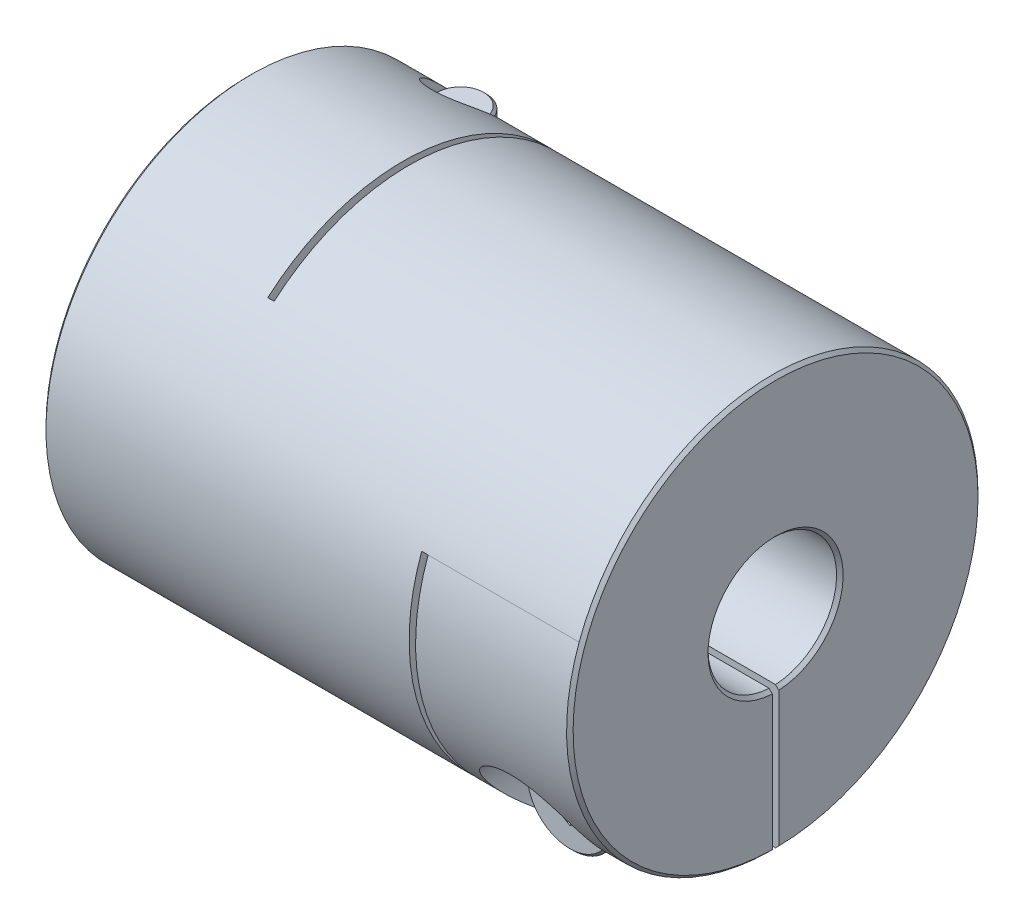
SolidWorks part; units mm, degrees
ref_plane "Front Plane" through (0, 0, 0) normal (0, 0, 1) x (1, 0, 0)
ref_plane "Top Plane" through (0, 0, 0) normal (0, 1, 0) x (1, 0, 0)
ref_plane "Right Plane" through (0, 0, 0) normal (1, 0, 0) x (0, 0, -1)
sketch "Sketch1" plane through (0, 0, 0) normal (1, 0, 0) x (0, 0, -1)
  circle A0 centre (0, 0) radius 16
  dimension "dim D" = 32
extrude "Boss-Extrude1" add sketch "Sketch1" along normal mid plane 41
sketch "Sketch2" plane through (20.5, 0, 0) normal (1, 0, 0) x (0, 0, -1)
  circle A0 centre (0, 0) radius 5
  dimension "dim D1" = 10
extrude "Cut-Extrude1" cut sketch "Sketch2" against normal through all
chamfer "Chamfer1" distance 0.254 angle 45 4 edges at (-20.5, 0, -5) (-20.5, 0, -16) (20.5, 0, -16) (20.5, 0, -5)
ref_plane "Plane2" through (0, -16, 0) normal (0, -1, 0) x (1, 0, 0)
ref_plane "L1" through (-14.5, 0, 0) normal (-1, 0, 0) x (0, 0, 1)
sketch "Sketch4" plane through (0, -16, 0) normal (0, -1, 0) x (1, 0, 0)
  line L0 (-20.246, -16) -> (20.246, -16) construction
  line L1 (-8.5, -16) -> (-8, -16)
  line L2 (-8.5, -16) -> (-8.5, 10.5)
  line L3 (-8.5, 10.5) -> (-8, 10.5)
  line L4 (-8, -16) -> (-8, 10.5)
  line L5 (-8.5, 5) -> (-8.5, 16) construction
  line L6 (20.246, 5) -> (-20.246, 5) construction
  line L7 (20.246, 16) -> (-20.246, 16) construction
  line L10 (-8.5, 10.5) -> (-20.5, 10.5) construction
  line L11 (-20.5, 15.746) -> (-20.5, -15.746) construction
  line L12 (-14.5, 10.2256) -> (-14.5, -10.2256) construction
  point P16 (-14.5, 10.5)
  dimension "D1" = 0.5
extrude "Cut-Extrude2" cut sketch "Sketch4" against normal through all
ref_plane "Plane4" through (0, 0, -16) normal (0, 0, -1) x (-1, 0, 0)
sketch "Sketch7" plane through (0, 0, -16) normal (0, 0, -1) x (-1, 0, 0)
  line L1 (-8, -16) -> (-8.5, -16)
  line L2 (-8.5, -16) -> (-8.5, 5.5)
  line L3 (-8.5, 5.5) -> (-8, 5.5)
  line L4 (-8, -16) -> (-8, 5.5)
  line L5 (20.5, 8.6487) -> (14.5, 8.6487) construction
  line L7 (-10.505, -16) -> (10.505, -16) construction
  line L8 (-20.246, -5) -> (8, -5) construction
  line L9 (20.5, -15.746) -> (20.5, 15.746) construction
  line L10 (-20.246, -5) -> (8, -5) construction
  line L11 (8, 12.0727) -> (8.5, 12.0727) construction
  line L12 (-8.5, 5.5) -> (-8.5, -16) construction
  line L14 (-20.246, -5) -> (8, -5) construction
  line L16 (-20.246, -5) -> (8, -5) construction
  line L17 (8.5, -16) -> (20.246, -16) construction
  line L18 (14.5, -10.2256) -> (14.5, 10.2256) construction
  line L19 (-20.246, -16) -> (-20.246, 16) construction
  line L20 (-20.5, 5.5) -> (-14.5, 5.5) construction
  line L21 (-20.5, 15.746) -> (-20.5, -15.746) construction
  line L22 (-14.5, 5.5) -> (-8.5, 5.5) construction
  line L23 (-20.246, -16) -> (-20.246, 16) construction
  line L24 (-20.246, -5) -> (-20.246, 16) construction
  line L25 (-20.246, -5) -> (8, -5) construction
  point P23 (-8.5, 5.5)
  point P33 (-20.246, 5.5)
extrude "Cut-Extrude3" cut sketch "Sketch7" against normal through all
sketch "Sketch8" plane through (0, 0, 0) normal (0, 1, 0) x (1, 0, 0)
  line L0 (-8.5, -10.5) -> (-8.5, 16) construction
  line L1 (-20.5, 16) -> (-8.5, 16)
  line L2 (-20.5, 16) -> (-20.5, 0)
  line L3 (-20.5, 0) -> (-8.5, 0)
  line L4 (-8.5, 16) -> (-8.5, 0)
  line L5 (10.505, 16) -> (-10.505, 16) construction
  line L6 (-20.5, 15.746) -> (-20.5, -15.746) construction
extrude "Cut-Extrude5" cut sketch "Sketch8" against normal mid plane 0.5
sketch "Sketch13" plane through (0, 0, 0) normal (0, 0, 1) x (1, 0, 0)
  line L0 (20.5, -15.746) -> (20.5, 15.746) construction
  line L1 (8.5, -16) -> (20.5, -16)
  line L2 (8.5, -16) -> (8.5, 0)
  line L3 (8.5, 0) -> (20.5, 0)
  line L4 (20.5, -16) -> (20.5, 0)
extrude "Cut-Extrude6" cut sketch "Sketch13" against normal mid plane 0.5
hole_wizard "CBORE for M4 SHCS1" positions "Sketch12" profile "Sketch11" counterbore size "M4" standard "Ansi Metric" end condition through all
sketch "Sketch12" plane through (0, -16, 0) normal (0, -1, 0) x (1, 0, 0)
  line L0 (-14.5, 10.2256) -> (-14.5, -10.2256) construction
  line L1 (-8.5, -4.9937) -> (-8.5, -15.998) construction
  line L2 (-8.5, -4.9937) -> (-8.5, -15.998)
  line L3 (-8.5, -10.4959) -> (-14.5, -10.4959) construction
  point P0 (-14.5, -10.4959)
sketch "Sketch11" plane through (-14.5, -16, -10.4959) normal (1, 0, 0) x (0, 0, -1)
  line L0 (0, 0) -> (0, 32)
  line L1 (0, 32) -> (2.25, 32)
  line L3 (2.25, 32) -> (2.25, 10)
  line L4 (2.25, 10) -> (4, 10)
  line L5 (4, 10) -> (4, 0)
  line L7 (4, 0) -> (0, 0)
  line L11 (0, -6.35) -> (0, 107.95) construction
  dimension "Thru Hole Dia." = 4.5
  dimension "Thru Hole Depth" = 32
  dimension "C'Bore Dia." = 8
  dimension "C'Bore Depth" = 10
ref_plane "Plane5" through (0, 0, 16) normal (0, 0, 1) x (1, 0, 0)
hole_wizard "CBORE for M4 SHCS2" positions "Sketch15" profile "Sketch14" counterbore size "M4" standard "Ansi Metric" end condition through all
sketch "Sketch15" plane through (0, 0, 16) normal (0, 0, 1) x (1, 0, 0)
  line L0 (-18.5, -6) -> (-10.5, -6) construction
  line L1 (-18.5, -6) -> (-10.5, -6)
  line L5 (0, 0) -> (0, 16) construction
  line L6 (-8.5, 16) -> (-20.246, 16) construction
  line L8 (18.5, -6) -> (10.5, -6)
  line L9 (14.5, -6) -> (14.5, -10.4959) construction
  line L11 (14.5, -15.998) -> (14.5, -4.9937) construction
  line L12 (20.246, -15.998) -> (8.5, -15.998) construction
  line L13 (8.5, -4.9937) -> (20.246, -4.9937) construction
  point P0 (14.5, -10.4959)
sketch "Sketch14" plane through (14.5, -10.4959, 16) normal (1, 0, 0) x (0, -1, 0)
  line L0 (0, 0) -> (0, 32)
  line L1 (0, 32) -> (2.25, 32)
  line L3 (2.25, 32) -> (2.25, 10)
  line L4 (2.25, 10) -> (4, 10)
  line L5 (4, 10) -> (4, 0)
  line L7 (4, 0) -> (0, 0)
  line L11 (0, -6.35) -> (0, 107.95) construction
  dimension "Thru Hole Dia." = 4.5
  dimension "Thru Hole Depth" = 32
  dimension "C'Bore Dia." = 8
  dimension "C'Bore Depth" = 10
sketch "Sketch16" plane through (0, 0, 6) normal (0, 0, 1) x (1, 0, 0)
  circle A0 centre (14.5, -10.4959) radius 3.5
  dimension "screw dia" = 7
extrude "Boss-Extrude2" add sketch "Sketch16" along normal blind 4 separate body
sketch "Sketch17" plane through (0, 0, 6) normal (0, 0, -1) x (-1, 0, 0)
  circle A0 centre (-14.5, -10.4959) radius 2
  dimension "D1" = 4
extrude "Boss-Extrude3" add sketch "Sketch17" along normal blind 17.5
chamfer "Chamfer2" distance 0.2 angle 45 3 edges at (12.5, -10.4959, -11.5) (18, -10.4959, 6) (18, -10.4959, 10)
sketch "Sketch18" plane through (0, 0, 10) normal (0, 0, 1) x (1, 0, 0)
  line L1 (14.5, -12.2279) -> (16, -11.3619)
  line L2 (16, -11.3619) -> (16, -9.6299)
  line L3 (16, -9.6299) -> (14.5, -8.7638)
  line L4 (14.5, -8.7638) -> (13, -9.6299)
  line L5 (13, -9.6299) -> (13, -11.3619)
  line L6 (13, -11.3619) -> (14.5, -12.2279)
  circle A0 centre (14.5, -10.4959) radius 1.5 construction
  dimension "hex" = 3
extrude "Cut-Extrude7" cut sketch "Sketch18" against normal blind 1.5
mirror "Mirror1" about plane through (0, 0, 0) normal (1, 0, 0) of bodies 121
pattern_circular "CirPattern1" count 2 every 90 about axis through (0, 0, 0) along (1, 0, 0) of bodies 122
delete or keep bodies "Body-Delete1" type delete bodies bodies 122
